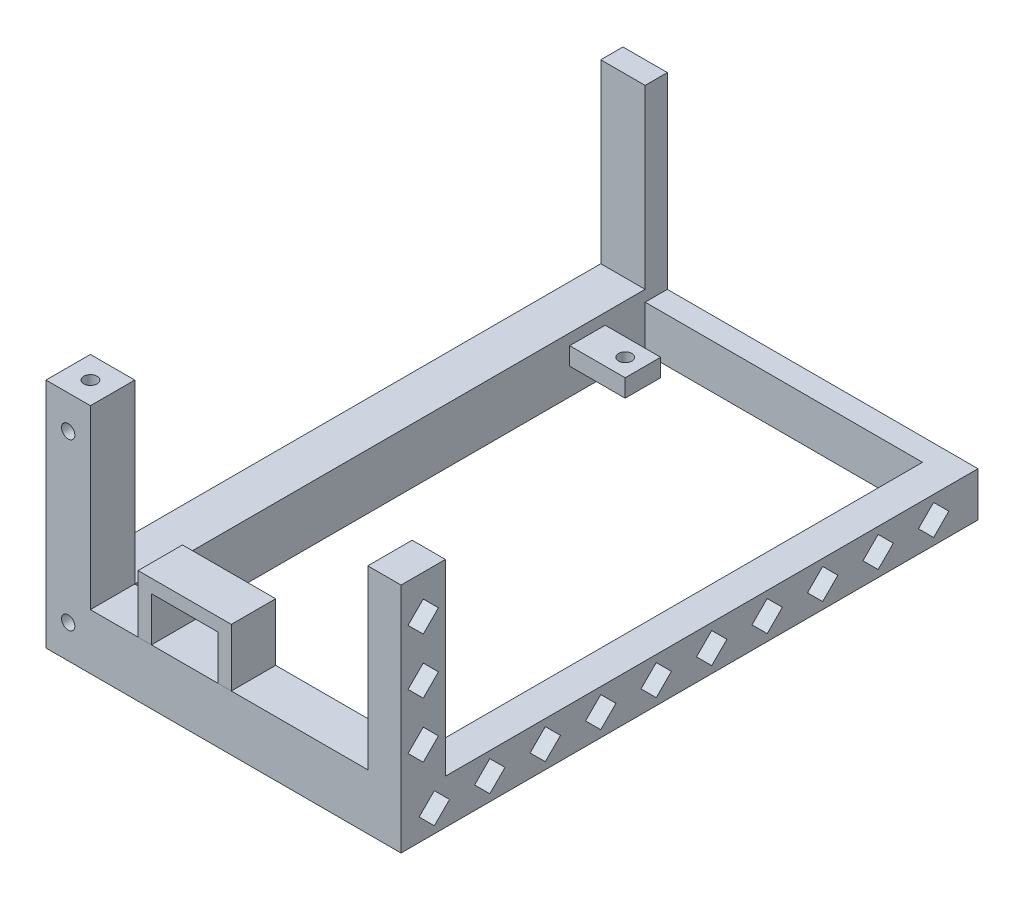
SolidWorks part; units mm, degrees
ref_plane "Front Plane" through (0, 0, 0) normal (0, 0, 1) x (1, 0, 0)
ref_plane "Top Plane" through (0, 0, 0) normal (0, 1, 0) x (1, 0, 0)
ref_plane "Right Plane" through (0, 0, 0) normal (1, 0, 0) x (0, 0, -1)
sketch "Sketch1" plane through (0, 0, 0) normal (0, 1, 0) x (1, 0, 0)
  line L0 (0, 0) -> (-45, 0) construction
  line L1 (35, -65) -> (-45, -65)
  line L2 (35, -65) -> (35, 65)
  line L3 (35, 65) -> (-45, 65)
  line L4 (-45, -65) -> (-45, 65)
  line L5 (0, 0) -> (35, 0) construction
  point P0 (0, 0)
  dimension "D1" = 65
  dimension "D2" = 65
extrude "Boss-Extrude1" add sketch "Sketch1" along normal blind 10
sketch "Sketch2" plane through (0, 10, 0) normal (0, 1, 0) x (1, 0, 0)
  line L0 (35, -65) -> (-45, -65)
  line L1 (-45, -65) -> (-45, 65)
  line L2 (-45, 65) -> (-35, 65)
  line L3 (35, 65) -> (-45, 65) construction
  line L4 (35, -65) -> (35, -55)
  line L5 (35, -65) -> (35, 65) construction
  line L6 (-35, 65) -> (-35, -55)
  line L7 (-35, -55) -> (35, -55)
extrude "Boss-Extrude2" add sketch "Sketch2" along normal blind 42.3
sketch "Sketch3" plane through (35, 0, 0) normal (1, 0, 0) x (0, 0, -1)
  line L1 (20.925, 5) -> (17.5, 8.425)
  line L39 (-55, 10) -> (-65, 10) construction
  line L40 (17.5, 8.425) -> (14.075, 5)
  line L41 (14.075, 5) -> (17.5, 1.575)
  line L42 (17.5, 1.575) -> (20.925, 5)
  line L56 (-65, 52.3) -> (-65, 0) construction
  line L57 (33.425, 5) -> (30, 8.425)
  line L58 (-55, 10) -> (-55, 0) construction
  line L73 (-65, 0) -> (65, 0) construction
  line L74 (30, 8.425) -> (26.575, 5)
  line L75 (-55, 5) -> (65, 5) construction
  line L76 (26.575, 5) -> (30, 1.575)
  line L77 (65, 10) -> (65, 0) construction
  line L118 (5, 8.425) -> (5, 1.575) construction
  line L119 (5, 8.425) -> (1.575, 5)
  line L120 (1.575, 5) -> (5, 1.575)
  line L121 (5, 1.575) -> (8.425, 5)
  line L122 (8.425, 5) -> (5, 8.425)
  line L139 (-4.075, 5) -> (-7.5, 8.425)
  line L140 (-7.5, 8.425) -> (-10.925, 5)
  line L141 (-10.925, 5) -> (-7.5, 1.575)
  line L142 (-7.5, 1.575) -> (-4.075, 5)
  line L143 (-16.575, 5) -> (-20, 8.425)
  line L144 (-20, 8.425) -> (-23.425, 5)
  line L145 (-23.425, 5) -> (-20, 1.575)
  line L146 (-20, 1.575) -> (-16.575, 5)
  line L147 (-29.075, 5) -> (-32.5, 8.425)
  line L148 (-32.5, 8.425) -> (-35.925, 5)
  line L149 (-35.925, 5) -> (-32.5, 1.575)
  line L150 (-32.5, 1.575) -> (-29.075, 5)
  line L151 (-41.575, 5) -> (-45, 8.425)
  line L152 (-45, 8.425) -> (-48.425, 5)
  line L153 (-48.425, 5) -> (-45, 1.575)
  line L154 (-45, 1.575) -> (-41.575, 5)
  line L155 (-54.075, 5) -> (-57.5, 8.425)
  line L156 (-57.5, 8.425) -> (-60.925, 5)
  line L157 (-60.925, 5) -> (-57.5, 1.575)
  line L158 (-57.5, 1.575) -> (-54.075, 5)
  line L159 (-60, 10) -> (-60, 52.3) construction
  line L160 (-65, 52.3) -> (-55, 52.3) construction
  line L161 (-63.425, 31.15) -> (-56.575, 31.15) construction
  line L162 (-63.425, 31.15) -> (-60, 34.575)
  line L163 (-60, 34.575) -> (-56.575, 31.15)
  line L164 (-56.575, 31.15) -> (-60, 27.725)
  line L165 (-60, 27.725) -> (-63.425, 31.15)
  line L166 (-60, 40.225) -> (-63.425, 43.65)
  line L167 (-63.425, 43.65) -> (-60, 47.075)
  line L168 (-60, 47.075) -> (-56.575, 43.65)
  line L169 (-56.575, 43.65) -> (-60, 40.225)
  line L170 (-60, 15.225) -> (-63.425, 18.65)
  line L171 (-63.425, 18.65) -> (-60, 22.075)
  line L172 (-60, 22.075) -> (-56.575, 18.65)
  line L173 (-56.575, 18.65) -> (-60, 15.225)
  line L174 (30, 1.575) -> (33.425, 5)
  line L175 (45.925, 5) -> (42.5, 8.425)
  line L176 (42.5, 8.425) -> (39.075, 5)
  line L177 (39.075, 5) -> (42.5, 1.575)
  line L178 (42.5, 1.575) -> (45.925, 5)
  line L179 (58.425, 5) -> (55, 8.425)
  line L180 (55, 8.425) -> (51.575, 5)
  line L181 (51.575, 5) -> (55, 1.575)
  line L182 (55, 1.575) -> (58.425, 5)
  point P15 (5, 5)
  point P61 (-60, 31.15)
  dimension "D1" = 6
  dimension "D2" = 2
  dimension "D3" = 2
extrude "Cut-Extrude1" cut sketch "Sketch3" against normal blind 5.25
sketch "Sketch4" plane through (0, 10, 0) normal (0, 1, 0) x (1, 0, 0)
  line L0 (-35, 65) -> (-26.5, 65) construction
  line L1 (35, 65) -> (-35, 65) construction
  line L2 (-26.5, 65) -> (-26.5, 47) construction
  circle A0 centre (-26.5, 47) radius 1.5
extrude "Cut-Extrude2" cut sketch "Sketch4" against normal through all
sketch "Sketch5" plane through (0, 10, 0) normal (0, 1, 0) x (1, 0, 0)
  line L0 (-35, -55) -> (-35, 43)
  line L1 (27.5, 60) -> (-35, 60)
  line L3 (27.5, 60) -> (27.5, -55)
  line L4 (-35, -55) -> (27.5, -55)
  line L6 (35, -55) -> (35, 65) construction
  line L7 (35, -55) -> (-35, -55) construction
  line L8 (-35, 43) -> (-22.5, 43)
  line L10 (-35, -55) -> (-35, 65) construction
  line L11 (-35, 60) -> (-35, 51)
  line L12 (-35, 51) -> (-22.5, 51)
  line L13 (-22.5, 51) -> (-22.5, 43)
  point P0 (0, 0)
  dimension "D3" = 9
  dimension "D2" = 8
  dimension "D1" = 7.5
extrude "Cut-Extrude3" cut sketch "Sketch5" against normal through all
sketch "Sketch7" plane through (-35, 0, 0) normal (1, 0, 0) x (0, 0, -1)
  line L0 (-55, 52.3) -> (-55, 12.5)
  line L1 (-55, 52.3) -> (-55, 0) construction
  line L2 (-55, 12.5) -> (60, 12.5)
  line L3 (60, 12.5) -> (60, 52.3)
  line L4 (-55, 52.3) -> (65, 52.3) construction
  line L5 (60, 52.3) -> (-55, 52.3)
  line L6 (65, 52.3) -> (65, 10) construction
  line L7 (43, 0) -> (-55, 0) construction
  dimension "D1" = 5
  dimension "D2" = 12.5
extrude "Cut-Extrude4" cut sketch "Sketch7" against normal through all
sketch "Sketch8" plane through (0, 0, 55) normal (0, 0, -1) x (-1, 0, 0)
  line L0 (35, 12.5) -> (35, 52.3)
  line L1 (-35, 52.3) -> (45, 52.3) construction
  line L2 (35, 52.3) -> (-27.5, 52.3)
  line L7 (35, 12.5) -> (-27.5, 12.5)
  line L8 (-27.5, 12.5) -> (-27.5, 52.3)
extrude "Cut-Extrude5" cut sketch "Sketch8" against normal blind 10
sketch "Sketch9" plane through (0, 52.3, 0) normal (0, 1, 0) x (1, 0, 0)
  line L0 (-45, -60) -> (-40, -60) construction
  line L1 (-45, -55) -> (-45, -65) construction
  circle A0 centre (-40, -60) radius 1.5
extrude "Cut-Extrude6" cut sketch "Sketch9" against normal blind 4
sketch "Sketch10" plane through (0, 0, 0) normal (0, -1, 0) x (1, 0, 0)
  circle A0 centre (-40, 60) radius 1.5 construction
  circle A1 centre (-40, 60) radius 1.5
extrude "Cut-Extrude7" cut sketch "Sketch10" against normal blind 4
sketch "Sketch11" plane through (0, 0, 0) normal (0, -1, 0) x (1, 0, 0)
  line L0 (-35, -43) -> (-22.5, -43)
  line L1 (-22.5, -43) -> (-22.5, -51)
  line L2 (-22.5, -51) -> (-35, -51)
  line L3 (-35, -51) -> (-35, -43)
extrude "Cut-Extrude8" cut sketch "Sketch11" against normal blind 6
sketch "Sketch13" plane through (0, 0, 65) normal (0, 0, 1) x (1, 0, 0)
  line L4 (-21.25, 12.5) -> (-6.25, 12.5)
  line L5 (27.5, 12.5) -> (-35, 12.5) construction
  line L15 (-21.25, 12.5) -> (-21.25, 22.5)
  line L16 (-21.25, 22.5) -> (-6.25, 22.5)
  line L17 (-6.25, 22.5) -> (-6.25, 12.5)
  line L20 (-3.25, 12.5) -> (-3.25, 25.5)
  line L21 (-3.25, 25.5) -> (-24.25, 25.5)
  line L22 (-24.25, 25.5) -> (-24.25, 12.5)
  line L23 (-24.25, 12.5) -> (-21.25, 12.5)
  line L24 (-6.25, 12.5) -> (-3.25, 12.5)
  point P8 (-13.75, 12.5)
  dimension "D1" = 3
  dimension "D2" = 3
  dimension "D3" = 3
extrude "Boss-Extrude3" add sketch "Sketch13" against normal blind 10 separate body
sketch "Sketch14" plane through (0, 0, 65) normal (0, 0, 1) x (1, 0, 0)
  line L0 (-40, 52.3) -> (-40, 44.8) construction
  line L1 (-45, 52.3) -> (-35, 52.3) construction
  line L2 (-40, 0) -> (-40, 7.5) construction
  line L3 (-45, 0) -> (35, 0) construction
  line L4 (-40, 7.5) -> (-45, 7.5) construction
  line L5 (-45, 52.3) -> (-45, 0) construction
  line L6 (-40, 44.8) -> (-45, 44.8) construction
  circle A0 centre (-40, 44.8) radius 1.5
  circle A1 centre (-40, 7.5) radius 1.5
extrude "Cut-Extrude9" cut sketch "Sketch14" against normal blind 4 contours A0 | A1
